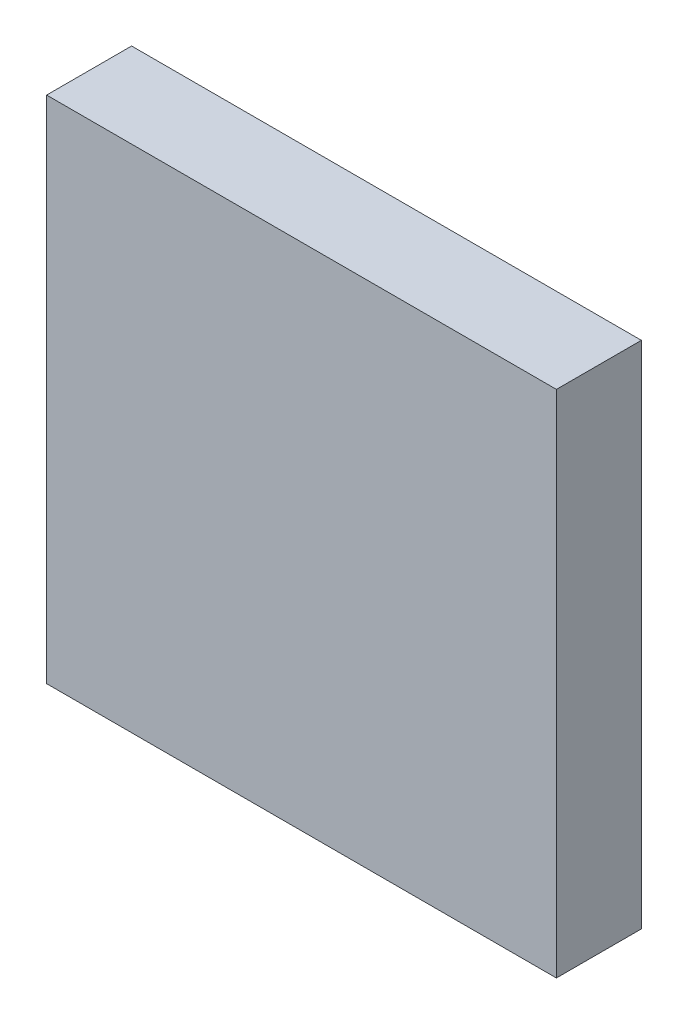
SolidWorks part; units mm, degrees
ref_plane "Piano frontale" through (0, 0, 0) normal (0, 0, 1) x (1, 0, 0)
ref_plane "Piano superiore" through (0, 0, 0) normal (0, 1, 0) x (1, 0, 0)
ref_plane "Piano destro" through (0, 0, 0) normal (1, 0, 0) x (0, 0, -1)
sketch "Schizzo1" plane through (0, 0, 0) normal (0, 0, 1) x (1, 0, 0)
  line L1 (-30, -30) -> (30, -30)
  line L2 (-30, -30) -> (-30, 30)
  line L3 (-30, 30) -> (30, 30)
  line L4 (30, -30) -> (30, 30)
  line L5 (-30, -30) -> (30, 30) construction
  line L6 (-30, 30) -> (30, -30) construction
  point P0 (0, 0)
  dimension "D1" = 60
  dimension "D2" = 60
extrude "Estrusione-Estrusione1" add sketch "Schizzo1" along normal blind 10
